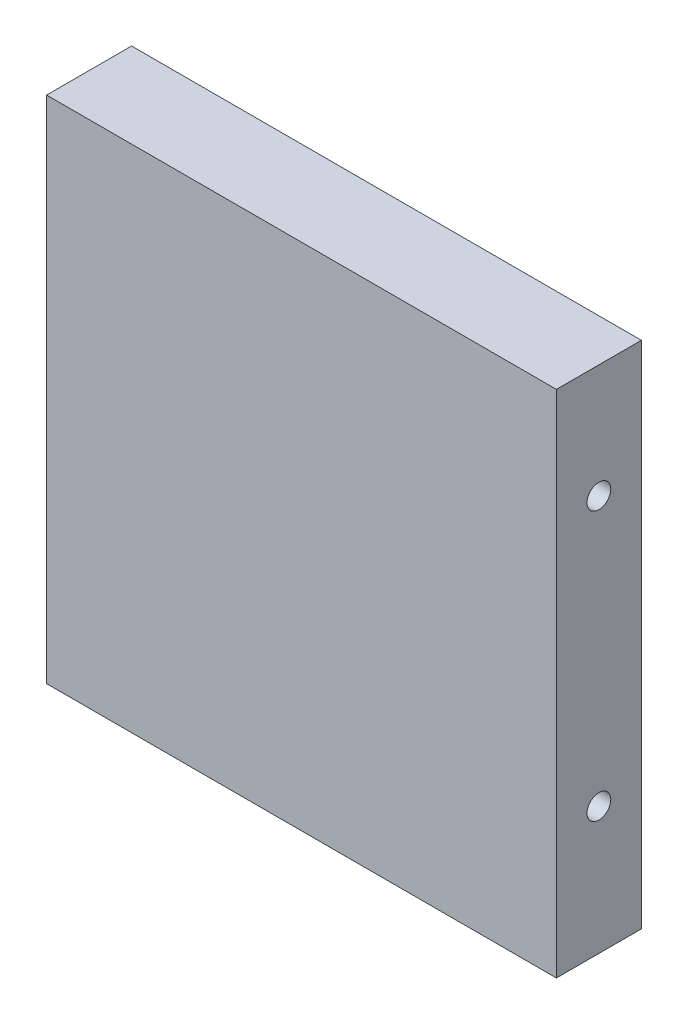
SolidWorks part; units mm, degrees
ref_plane "Front Plane" through (0, 0, 0) normal (0, 0, 1) x (1, 0, 0)
ref_plane "Top Plane" through (0, 0, 0) normal (0, 1, 0) x (1, 0, 0)
ref_plane "Right Plane" through (0, 0, 0) normal (1, 0, 0) x (0, 0, -1)
sketch "Sketch1" plane through (0, 0, 0) normal (0, 0, 1) x (1, 0, 0)
  line L1 (-19.05, -19.05) -> (19.05, -19.05)
  line L2 (-19.05, -19.05) -> (-19.05, 19.05)
  line L3 (-19.05, 19.05) -> (19.05, 19.05)
  line L4 (19.05, -19.05) -> (19.05, 19.05)
  line L5 (-19.05, -19.05) -> (19.05, 19.05) construction
  line L6 (-19.05, 19.05) -> (19.05, -19.05) construction
  point P0 (0, 0)
  dimension "D1" = 38.1
  dimension "D2" = 38.1
extrude "Boss-Extrude1" add sketch "Sketch1" along normal blind 6.35
hole_wizard "Tap Drill for #2-64 Tap1" positions "Sketch3" profile "Sketch2" hole size "#2-64" standard "ANSI Inch"
sketch "Sketch3" plane through (0, -19.05, 0) normal (0, -1, 0) x (-1, 0, 0)
  point P0 (-15.24, -2.6029)
  point P3 (15.24, -2.6029)
sketch "Sketch2" plane through (15.24, -19.05, 2.6029) normal (1, 0, 0) x (0, 0, -1)
  line L0 (0, 0) -> (0, 8.1542)
  line L1 (0, 8.1542) -> (0.889, 7.62)
  line L2 (0.889, 7.62) -> (0.889, 0)
  line L5 (0.889, 0) -> (0, 0)
  line L10 (0, 8.1542) -> (-0.889, 7.62) construction
  line L11 (0, -6.35) -> (0, 107.95) construction
  dimension "Hole Dia." = 1.778
  dimension "Hole Depth" = 7.62
  dimension "Drill Angle" = 118
hole_wizard "Tap Drill for #2-64 Tap2" positions "Sketch5" profile "Sketch4" hole size "#2-64" standard "ANSI Inch"
sketch "Sketch5" plane through (19.05, 0, 0) normal (1, 0, 0) x (0, 0, -1)
  circle A0 centre (-3.175, 9.525) radius 1.0414 construction
  point P0 (-3.175, 10.5664)
  point P4 (-3.175, -9.525)
sketch "Sketch4" plane through (19.05, 10.5664, 3.175) normal (0, 1, 0) x (0, 0, -1)
  line L0 (0, 0) -> (0, 8.1542)
  line L1 (0, 8.1542) -> (0.889, 7.62)
  line L2 (0.889, 7.62) -> (0.889, 0)
  line L5 (0.889, 0) -> (0, 0)
  line L10 (0, 8.1542) -> (-0.889, 7.62) construction
  line L11 (0, -6.35) -> (0, 107.95) construction
  dimension "Hole Dia." = 1.778
  dimension "Hole Depth" = 7.62
  dimension "Drill Angle" = 118
